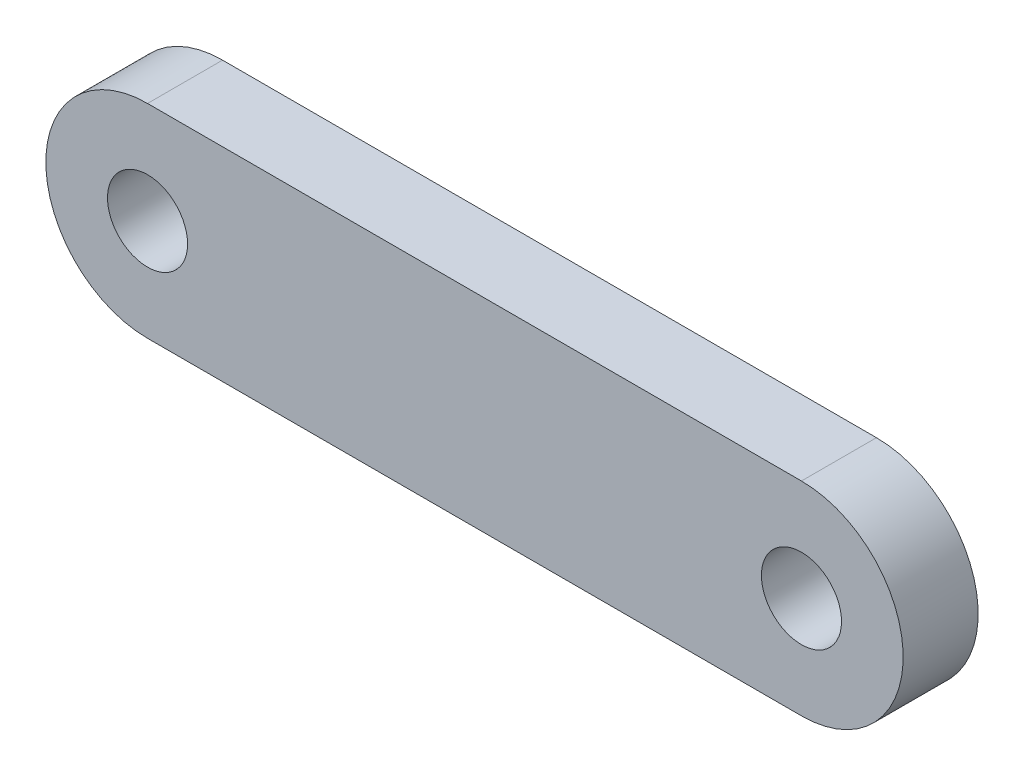
SolidWorks part; units mm, degrees
ref_plane "Front Plane" through (0, 0, 0) normal (0, 0, 1) x (1, 0, 0)
ref_plane "Top Plane" through (0, 0, 0) normal (0, 1, 0) x (1, 0, 0)
ref_plane "Right Plane" through (0, 0, 0) normal (1, 0, 0) x (0, 0, -1)
sketch "Sketch1" plane through (0, 0, 0) normal (0, 0, 1) x (1, 0, 0)
  line L0 (25.7175, 0) -> (-25.7175, 0) construction
  line L1 (25.7175, -8) -> (-25.7175, -8)
  line L2 (25.7175, 8) -> (-25.7175, 8)
  arc A0 (25.7175, -8) -> (25.7175, 8) centre (25.7175, 0) ccw
  arc A1 (-25.7175, 8) -> (-25.7175, -8) centre (-25.7175, 0) ccw
  circle A2 centre (25.7175, 0) radius 3.15
  circle A3 centre (-25.7175, 0) radius 3.15
  point P2 (0, 0)
  dimension "D3" = 6.3
  dimension "D1" = 16
  dimension "D2" = 51.435
extrude "Boss-Extrude1" add sketch "Sketch1" along normal blind 5.9
move or copy body "Body-Move/Copy1" [suppressed] bodies to move or copy 101
